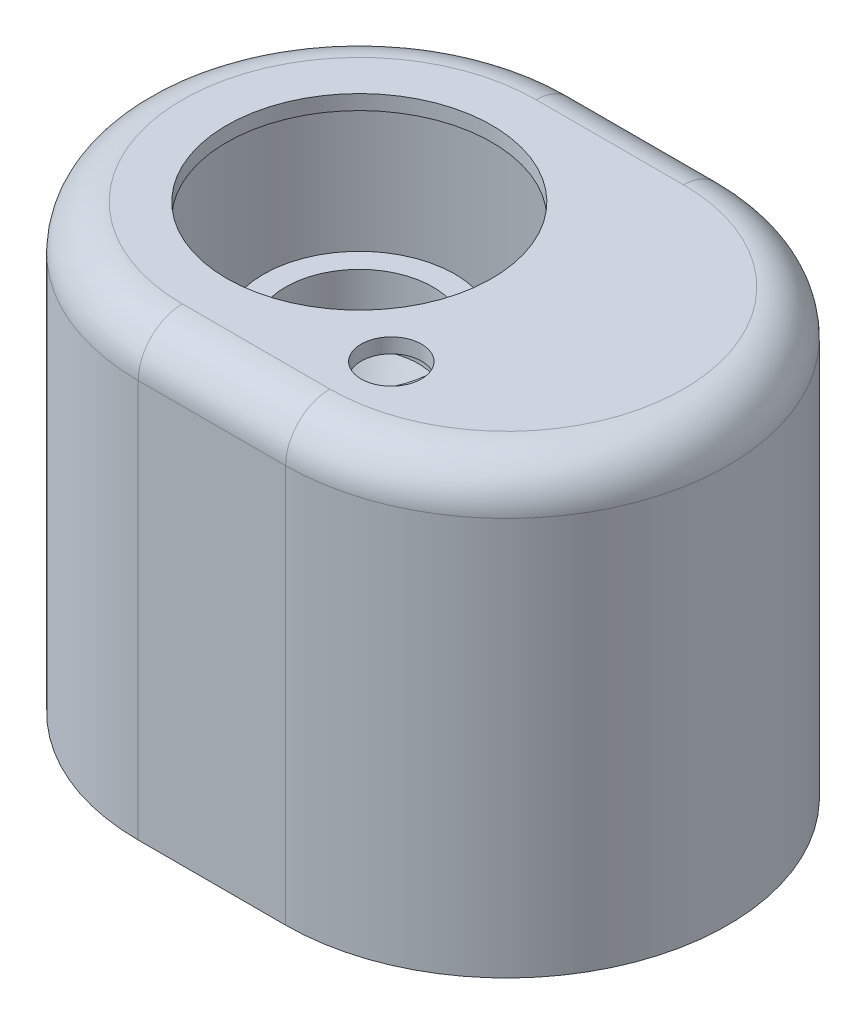
SolidWorks part; units mm, degrees
ref_plane "前视基准面" through (0, 0, 0) normal (0, 0, 1) x (1, 0, 0)
ref_plane "上视基准面" through (0, 0, 0) normal (0, 1, 0) x (1, 0, 0)
ref_plane "右视基准面" through (0, 0, 0) normal (1, 0, 0) x (0, 0, -1)
sketch "草图2" plane through (0, 0, 0) normal (0, 1, 0) x (1, 0, 0)
  line L0 (0, 0) -> (20, 0) construction
  line L1 (0, 30) -> (20, 30)
  line L2 (0, -30) -> (20, -30)
  arc A0 (0, 30) -> (0, -30) centre (0, 0) ccw
  arc A1 (20, -30) -> (20, 30) centre (20, 0) ccw
  point P2 (10, 0)
  dimension "D1" = 60
  dimension "D2" = 20
extrude "凸台-拉伸2" add sketch "草图2" along normal blind 60 and the other way blind 0.0001
fillet "圆角2" radius 6 4 edges at (10, 60, -30) (50, 60, 0) (10, 60, 30) (-30, 60, 0)
shell "抽壳2" thickness 2
sketch "草图3" plane through (0, 60, 0) normal (0, 1, 0) x (1, 0, 0)
  circle A0 centre (0, 0) radius 18
  dimension "D1" = 36
extrude "切除-拉伸1" cut sketch "草图3" against normal up to next
sketch "草图4" plane through (0, 0, 0) normal (0, 0, 1) x (1, 0, 0)
  line L0 (0, 45) -> (-10, 45) construction
  line L1 (0, 54) -> (0, -0.0001) construction
  line L2 (-10, 45) -> (-10, 39)
  line L3 (-10, 39) -> (-8, 39)
  line L4 (-8, 39) -> (-8, 37)
  line L7 (-4.5, 30) -> (-6.5, 30)
  line L8 (-6.5, 30) -> (-6.5, 26)
  line L9 (-6.5, 26) -> (-9.5, 26)
  line L10 (-9.5, 26) -> (-9.5, 31.0557)
  line L11 (-9.5, 31.0557) -> (-13, 38.0557)
  line L12 (-13, 38.0557) -> (-13, 45)
  line L13 (-13, 45) -> (-10, 45)
  line L14 (-8, 37) -> (-4.5, 30)
  line L15 (18, 60) -> (-18, 60) construction
  line L16 (0, 72.7731) -> (0, 17.2269) construction
  line L17 (0, 48.7591) -> (0, 5.2548) construction
  point P21 (0, 45)
  dimension "D1" = 10
  dimension "D2" = 3
  dimension "D3" = 6
  dimension "D4" = 2
  dimension "D5" = 3
  dimension "D6" = 4
  dimension "D7" = 6.5
  dimension "D8" = 9
  dimension "D9" = 15
  dimension "D10" = 2
  dimension "D11" = 2
  dimension "D12" = 4
revolve "旋转3" add sketch "草图4" angle 360 about L16
ref_plane "基准面1" through (0, 33.2, 0) normal (0, 1, 0) x (1, 0, 0)
sketch "草图5" plane through (0, 33.2, 0) normal (0, 1, 0) x (1, 0, 0)
  line L0 (31, -19.5) -> (31, -33.5959) construction
  line L1 (34.15, -19.5) -> (34.15, -33.5959)
  line L2 (27.85, -19.5) -> (27.85, -33.5959)
  line L3 (31, 19.5) -> (31, 32.486) construction
  line L4 (27.85, 19.5) -> (27.85, 32.486)
  line L5 (34.15, 19.5) -> (34.15, 32.486)
  arc A0 (34.15, -19.5) -> (27.85, -19.5) centre (31, -19.5) ccw
  arc A1 (27.85, -33.5959) -> (34.15, -33.5959) centre (31, -33.5959) ccw
  arc A2 (27.85, 19.5) -> (34.15, 19.5) centre (31, 19.5) ccw
  arc A3 (34.15, 32.486) -> (27.85, 32.486) centre (31, 32.486) ccw
  arc A4 (20, -30) -> (20, 30) centre (20, 0) ccw construction
  arc A5 (20, -30) -> (20, 30) centre (20, 0) ccw
  circle A6 centre (31, -19.5) radius 1.5
  circle A7 centre (31, 19.5) radius 1.6114
  point P3 (31, -26.548)
  point P8 (31, 25.993)
  dimension "D1" = 6.3
  dimension "D2" = 6.3
extrude "凸台-拉伸5" add sketch "草图5" along normal up to body separate body contours L2 A5 L1 A0 A6 | L5 A5 L4 A2 A7
sketch "草图6" plane through (0, 60, 0) normal (0, 1, 0) x (1, 0, 0)
  circle A0 centre (20.9369, -16.594) radius 4.1
  dimension "D1" = 8.2
extrude "切除-拉伸2" cut sketch "草图6" against normal up to surface (2 mm away) up to face at (0, 58, 18)
ref_plane "基准面2" through (20, -0.0001, 28) normal (1, 0, 0) x (0, 0, -1)
sketch "草图8" plane through (0, -0.0001, 0) normal (0, -1, 0) x (1, 0, 0)
  line L2 (0, -30) -> (20, -30)
  line L3 (20, 30) -> (0, 30)
  line L4 (0, -30) -> (20, -30)
  line L5 (20, 30) -> (0, 30)
  line L6 (20, -28) -> (0, -28) construction
  line L7 (0, 28) -> (20, 28) construction
  line L8 (0, -26.5) -> (20, -26.5)
  line L9 (20, 26.5) -> (0, 26.5)
  line L10 (0, -26.5) -> (20, -26.5)
  line L11 (20, 26.5) -> (0, 26.5)
  line L12 (20, -28) -> (0, -28)
  line L13 (0, 28) -> (20, 28)
  arc A2 (0, 30) -> (0, -30) centre (0, 0) ccw
  arc A3 (20, -30) -> (20, 30) centre (20, 0) ccw
  arc A4 (0, 30) -> (0, -30) centre (0, 0) ccw
  arc A5 (20, -30) -> (20, 30) centre (20, 0) ccw
  arc A6 (0, 28) -> (0, -28) centre (0, 0) ccw construction
  arc A7 (20, -28) -> (20, 28) centre (20, 0) ccw construction
  arc A8 (0, 26.5) -> (0, -26.5) centre (0, 0) ccw
  arc A9 (20, -26.5) -> (20, 26.5) centre (20, 0) ccw
  arc A10 (0, 26.5) -> (0, -26.5) centre (0, 0) ccw
  arc A11 (20, -26.5) -> (20, 26.5) centre (20, 0) ccw
  arc A12 (0, 28) -> (0, -28) centre (0, 0) ccw
  arc A13 (20, -28) -> (20, 28) centre (20, 0) ccw
  line M9 (20, -28) -> (0, -28)
  arc M10 (0, -28) -> (0, 28) centre (0, 0) cw
  line M11 (0, 28) -> (20, 28)
  arc M12 (20, 28) -> (20, -28) centre (20, 0) cw
  dimension "D1" = 0
  dimension "D2" = 1.5
extrude "凸台-拉伸6" add sketch "草图8" against normal blind 4 from offset 2 contours A11 L10 A10 L11 M9 M12 M11 M10 offset against normal yes
sketch "草图10" plane through (0, 45, 0) normal (0, 1, 0) x (1, 0, 0)
  line L0 (9.1035, 26.4243) -> (9.1035, -26.5096)
